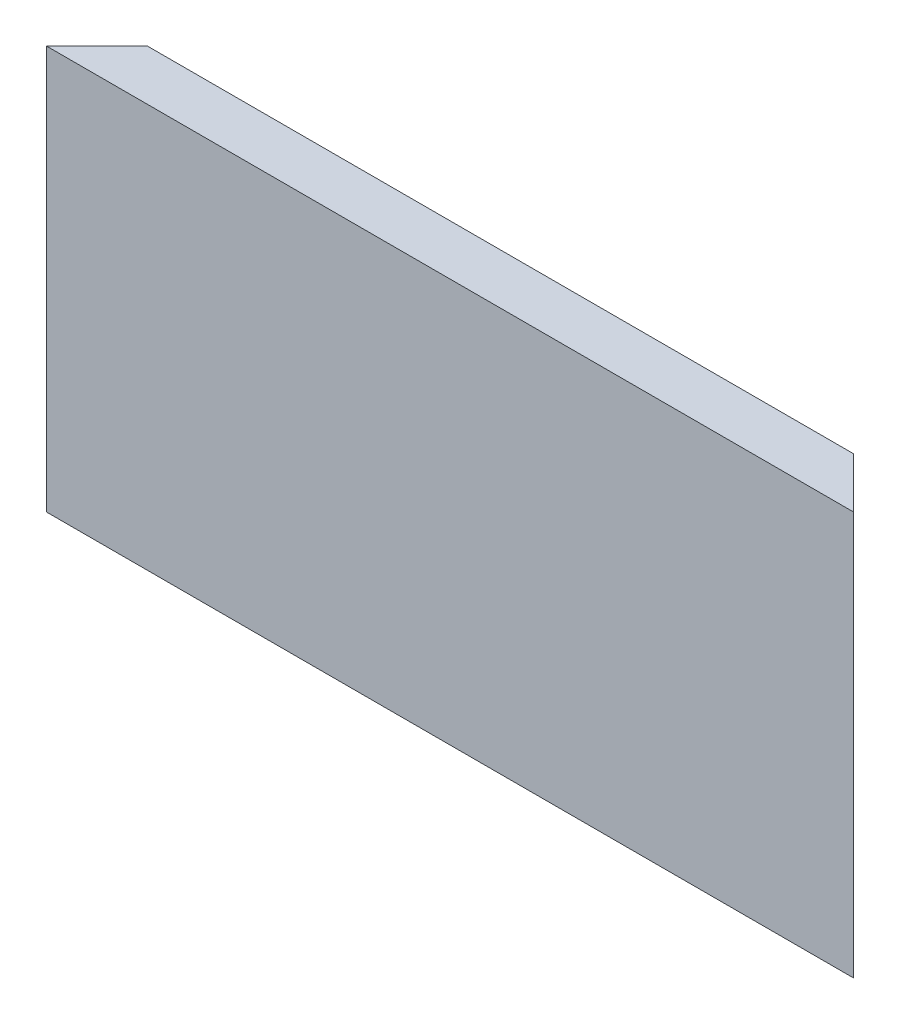
SolidWorks part; units mm, degrees
ref_plane "Front Plane" through (0, 0, 0) normal (0, 0, 1) x (1, 0, 0)
ref_plane "Top Plane" through (0, 0, 0) normal (0, 1, 0) x (1, 0, 0)
ref_plane "Right Plane" through (0, 0, 0) normal (1, 0, 0) x (0, 0, -1)
sketch "Sketch1" plane through (0, 0, 0) normal (1, 0, 0) x (0, 0, -1)
  line L0 (-2.5, -20) -> (2.5, -15)
  line L1 (-2.5, 20) -> (2.5, 20)
  line L2 (-2.5, 20) -> (-2.5, -20)
  line L4 (2.5, 20) -> (2.5, -15)
  line L5 (-2.5, 20) -> (2.5, -20) construction
  line L6 (-2.5, -20) -> (2.5, 20) construction
  point P0 (0, 0)
  dimension "D1" = 5
  dimension "D2" = 40
  dimension "D3" = 45
extrude "Boss-Extrude1" add sketch "Sketch1" along normal blind 80
sketch "Sketch2" plane through (0, 20, 0) normal (0, 1, 0) x (1, 0, 0)
  line L0 (80, 2.5) -> (0, 2.5) construction
  line L1 (80, 2.5) -> (75, 2.5)
  line L2 (0, -2.5) -> (5, 2.5)
  line L3 (80, -2.5) -> (0, -2.5) construction
  line L4 (80, -2.5) -> (75, 2.5)
  line L5 (80, 2.5) -> (80, -2.5) construction
  line L6 (80, 2.5) -> (80, -2.5)
  line L7 (0, 2.5) -> (0, -2.5) construction
  line L8 (0, 2.5) -> (0, -2.5)
  line L9 (5, 2.5) -> (0, 2.5)
  dimension "D1" = 45
  dimension "D2" = 45
extrude "Cut-Extrude1" cut sketch "Sketch2" against normal blind 80
sketch "Sketch3" plane through (0, 0, 0) normal (1, 0, 0) x (0, 0, -1)
  line L0 (2.5, -15) -> (2.5, 20) construction
  line L1 (-2.5, 20) -> (2.5, 20) construction
  line L2 (-2.5, 20) -> (-2.5, 10) construction
  line L3 (-2.5, 10) -> (2.5, 10) construction
  line L4 (2.5, 20) -> (2.5, 10) construction
  line L5 (-2.5, 15) -> (2.5, 15) construction
  line L7 (2.5, 16.5) -> (-0.5, 16.5)
  line L8 (2.5, 16.5) -> (2.5, 13.5)
  line L9 (2.5, 13.5) -> (-0.5, 13.5)
  line L10 (-0.5, 16.5) -> (-0.5, 13.5)
  dimension "D1" = 10
  dimension "D2" = 3
  dimension "D3" = 1.5
  dimension "D4" = 2
extrude "Cut-Extrude2" cut sketch "Sketch3" along normal through all both
